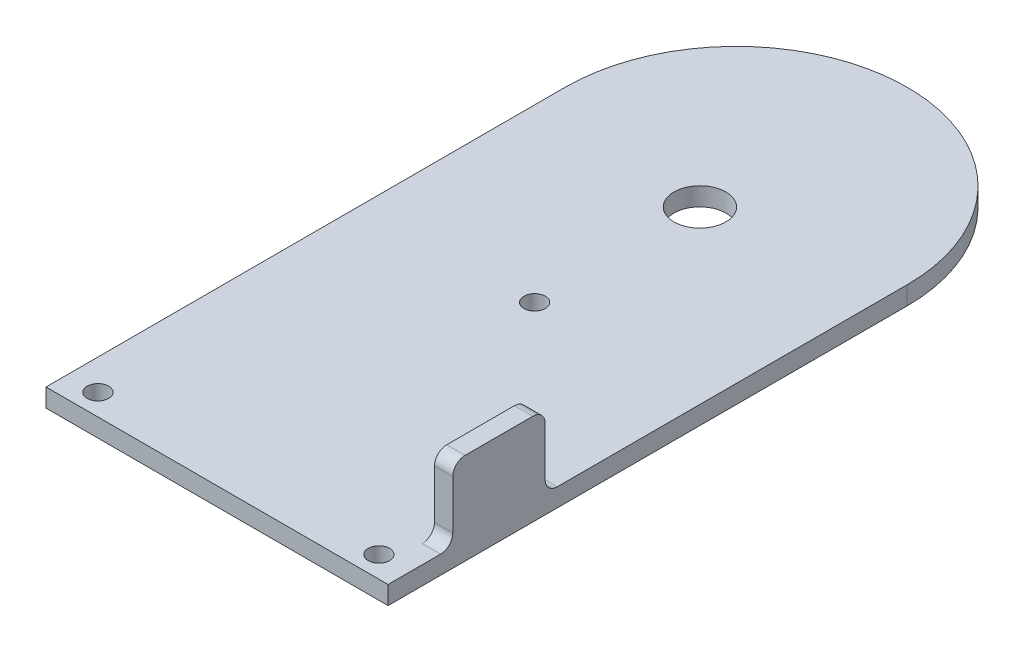
SolidWorks part; units mm, degrees
ref_plane "Front Plane" through (0, 0, 0) normal (0, 0, 1) x (1, 0, 0)
ref_plane "Top Plane" through (0, 0, 0) normal (0, 1, 0) x (1, 0, 0)
ref_plane "Right Plane" through (0, 0, 0) normal (1, 0, 0) x (0, 0, -1)
sketch "Sketch1" plane through (0, 0, 0) normal (0, 1, 0) x (1, 0, 0)
  line L2 (0, 0) -> (0, -85)
  line L3 (0, -85) -> (56, -85)
  line L4 (56, 0) -> (56, -85)
  arc A0 (56, 0) -> (0, 0) centre (28, 0) ccw
  circle A1 centre (5, -81.5) radius 1.75
  circle A2 centre (51, -81.5) radius 1.75
  circle A3 centre (28, -33) radius 1.75
  circle A5 centre (28, -5.94) radius 4.25
  dimension "D5" = 52
  dimension "D7" = 79.06
  dimension "D9" = 28
  dimension "D1" = 5
  dimension "D2" = 3.5
  dimension "D3" = 5
  dimension "D4" = 3.5
  dimension "D6" = 28
  dimension "D8" = 85
  dimension "D10" = 56
extrude "Boss-Extrude1" add sketch "Sketch1" along normal blind 3
sketch "Sketch2" plane through (0, 3, 0) normal (0, 1, 0) x (1, 0, 0)
  line L0 (56, -85) -> (56, 0) construction
  line L1 (56, -74.402) -> (53, -74.402)
  line L2 (56, -74.402) -> (56, -59.2863)
  line L3 (56, -59.2863) -> (53, -59.2863)
  line L4 (53, -74.402) -> (53, -59.2863)
extrude "Boss-Extrude2" add sketch "Sketch2" along normal blind 12
fillet "Fillet1" radius 2 4 edges at (54.5, 3, 74.402) (54.5, 3, 59.2863) (54.5, 15, 59.2863) (54.5, 15, 74.402)
